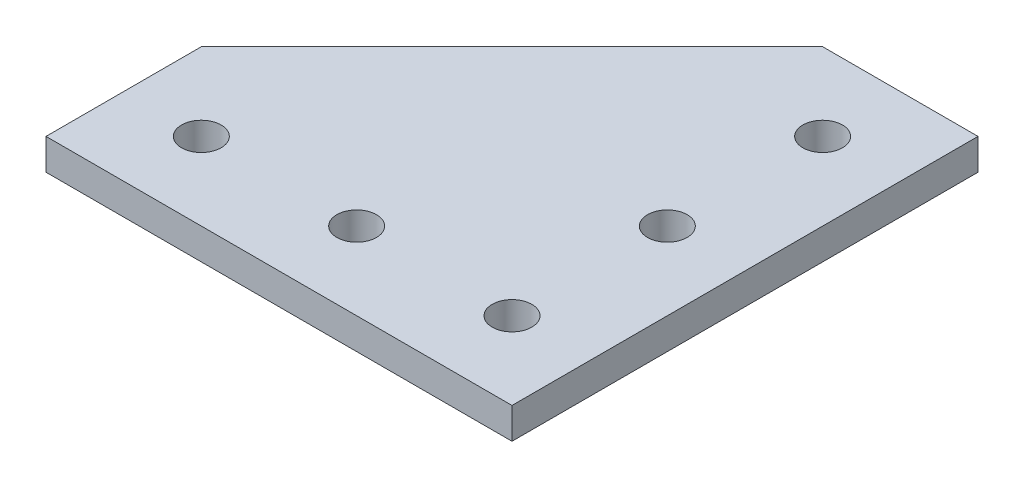
SolidWorks part; units mm, degrees
material "6061-T6 (SS)"
ref_plane "Front Plane" through (0, 0, 0) normal (0, 0, 1) x (1, 0, 0)
ref_plane "Top Plane" through (0, 0, 0) normal (0, 1, 0) x (1, 0, 0)
ref_plane "Right Plane" through (0, 0, 0) normal (1, 0, 0) x (0, 0, -1)
sketch "Sketch1" plane through (0, 0, 0) normal (0, 1, 0) x (1, 0, 0)
  line L0 (-50, 0) -> (0, 0) construction
  line L1 (10, -10) -> (-50, -10)
  line L2 (10, -10) -> (10, 50)
  line L3 (0, 0) -> (0, 50) construction
  line L4 (-50, -10) -> (-50, 10)
  line L5 (0, 0) -> (-20, 0) construction
  line L6 (0, 0) -> (0, 20) construction
  line L7 (-50, 10) -> (-10, 50)
  line L8 (-10, 50) -> (10, 50)
  circle A0 centre (-20, 0) radius 2.55
  circle A1 centre (-40, 0) radius 2.55
  circle A2 centre (0, 0) radius 2.55
  circle A3 centre (0, 20) radius 2.55
  circle A4 centre (0, 40) radius 2.55
  dimension "D3" = 3
  dimension "D2" = 5.1
  dimension "D1" = 20
  dimension "D4" = 20
  dimension "D5" = 60
  dimension "D7" = 20
  dimension "D6" = 3
extrude "Boss-Extrude1" add sketch "Sketch1" along normal blind 4
